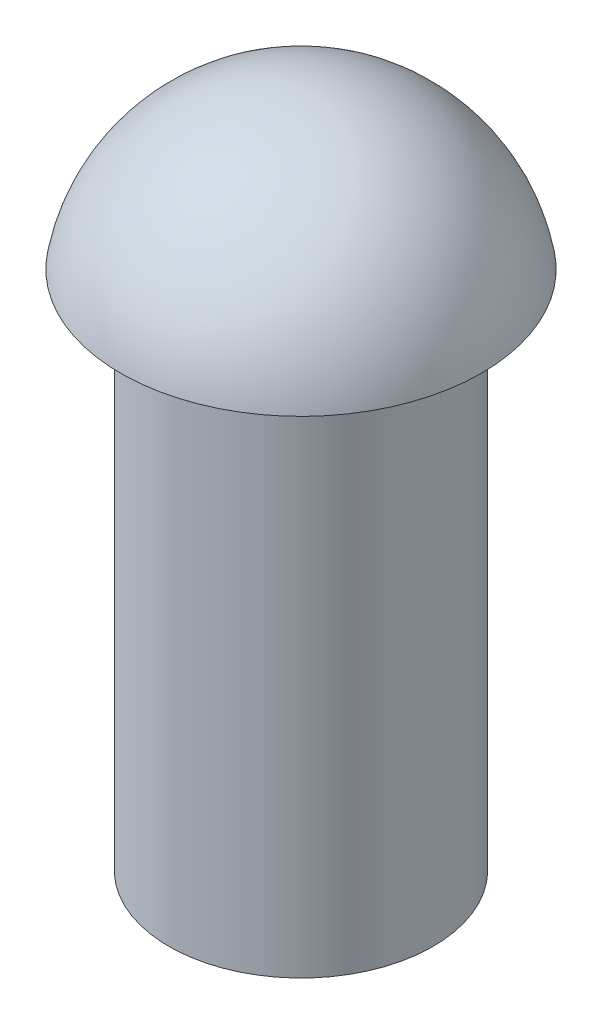
SolidWorks part; units mm, degrees
ref_plane "Front Plane" through (0, 0, 0) normal (0, 0, 1) x (1, 0, 0)
ref_plane "Top Plane" through (0, 0, 0) normal (0, 1, 0) x (1, 0, 0)
ref_plane "Right Plane" through (0, 0, 0) normal (1, 0, 0) x (0, 0, -1)
sketch "Sketch1" plane through (0, 0, 0) normal (0, 0, 1) x (1, 0, 0)
  line L0 (0, 0) -> (3.2311, 0)
  line L1 (3.2311, 0) -> (3.2311, 12.7396)
  line L2 (3.2311, 12.7396) -> (4.4152, 12.7396)
  line L3 (0, 0) -> (0, 16.4646)
  arc A0 (0, 16.4646) -> (4.4152, 12.7396) centre (0, 11.9854) cw
revolve "Revolve1" add sketch "Sketch1" angle 360 about L3
